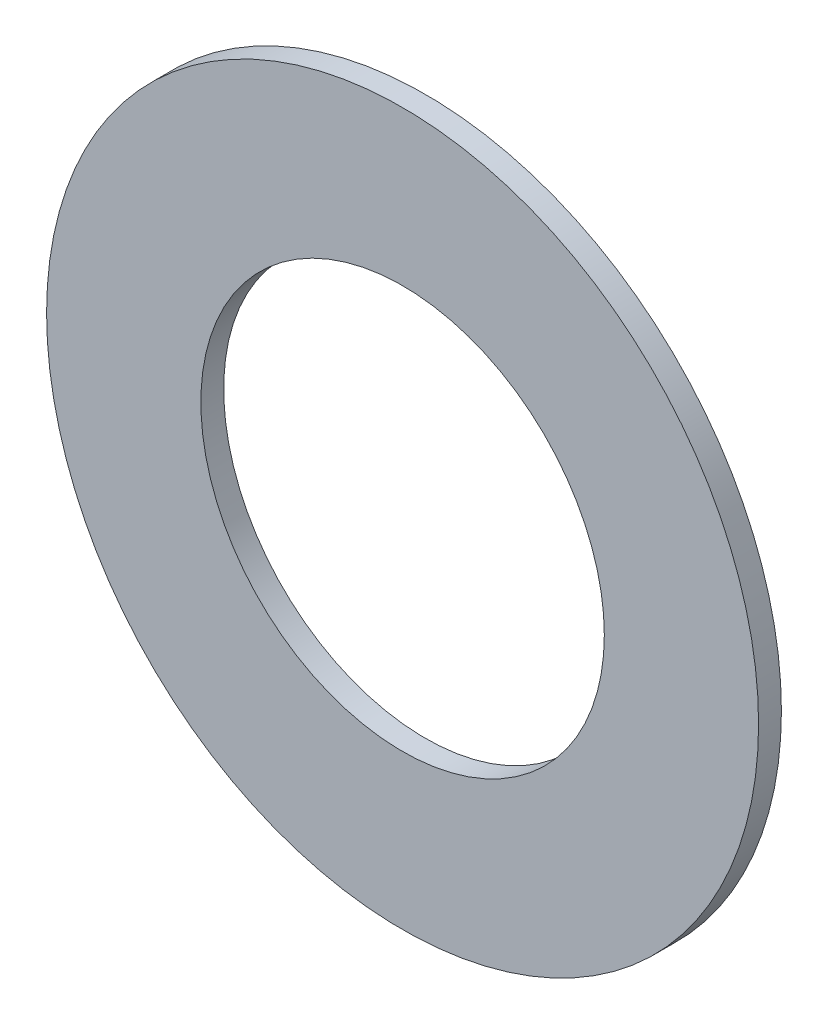
SolidWorks part; units mm, degrees
ref_plane "Front Plane" through (0, 0, 0) normal (0, 0, 1) x (1, 0, 0)
ref_plane "Top Plane" through (0, 0, 0) normal (0, 1, 0) x (1, 0, 0)
ref_plane "Right Plane" through (0, 0, 0) normal (1, 0, 0) x (0, 0, -1)
sketch "Sketch1" plane through (0, 0, 0) normal (0, 0, 1) x (1, 0, 0)
  circle A0 centre (0, 0) radius 49.53
  circle A1 centre (0, 0) radius 28.067
  dimension "D1" = 99.06
  dimension "D2" = 56.134
extrude "Boss-Extrude1" add sketch "Sketch1" along normal blind 3.175
